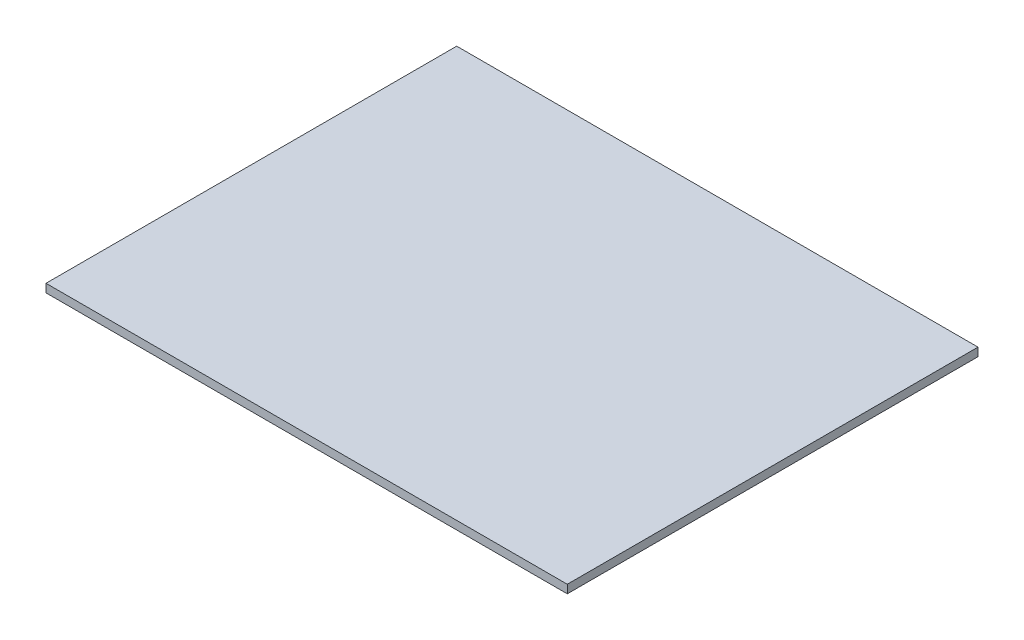
SolidWorks part; units mm, degrees
material "Placa de circuito de energia"
ref_plane "Plano frontal" through (0, 0, 0) normal (0, 0, 1) x (1, 0, 0)
ref_plane "Plano superior" through (0, 0, 0) normal (0, 1, 0) x (1, 0, 0)
ref_plane "Plano direito" through (0, 0, 0) normal (1, 0, 0) x (0, 0, -1)
sketch "Sketch1" plane through (0, 0, 0) normal (0, 1, 0) x (1, 0, 0)
  line L1 (-49.5, 39) -> (49.5, 39)
  line L2 (-49.5, 39) -> (-49.5, -39)
  line L3 (-49.5, -39) -> (49.5, -39)
  line L4 (49.5, 39) -> (49.5, -39)
  point P4 (0, 39)
  point P6 (-49.5, 0)
  dimension "D1" = 99
  dimension "D2" = 78
extrude "Boss-Extrude1" add sketch "Sketch1" along normal mid plane 1.58
